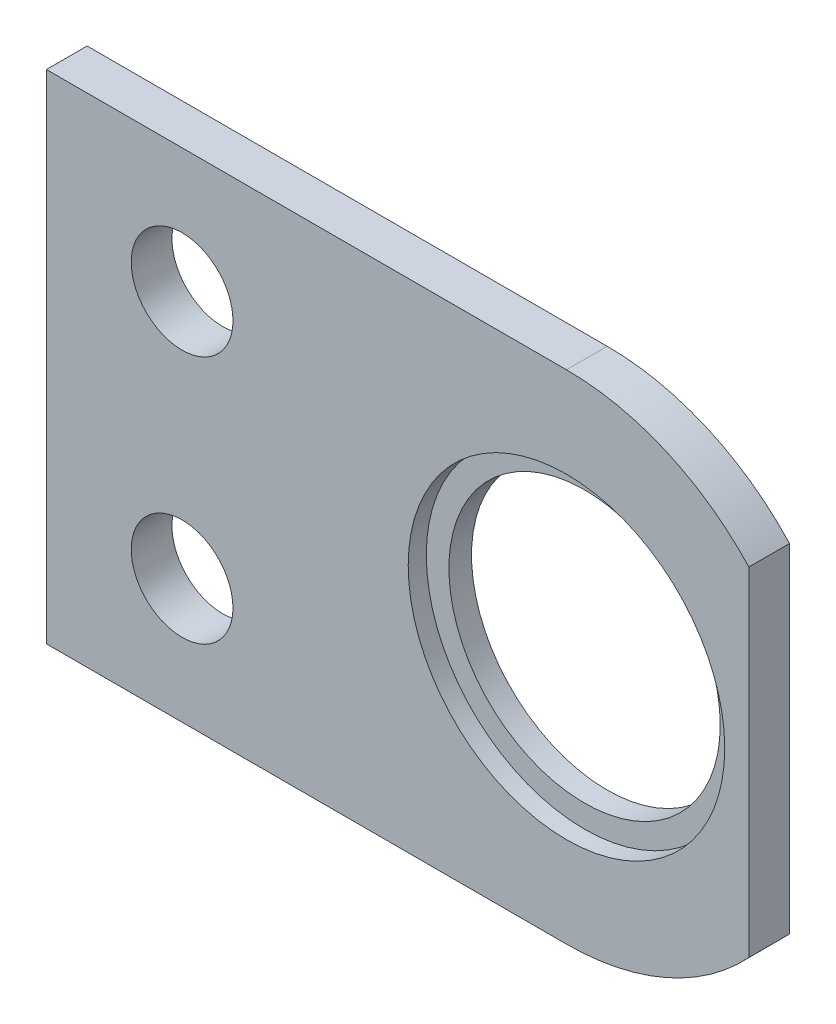
SolidWorks part; units mm, degrees
ref_plane "前视基准面" through (0, 0, 0) normal (0, 0, 1) x (1, 0, 0)
ref_plane "上视基准面" through (0, 0, 0) normal (0, 1, 0) x (1, 0, 0)
ref_plane "右视基准面" through (0, 0, 0) normal (1, 0, 0) x (0, 0, -1)
sketch "草图1" plane through (0, 0, 0) normal (0, 0, 1) x (1, 0, 0)
  line L0 (0, 7.4788) -> (0, -7.4788)
  line L1 (-31.0664, -11) -> (-8.0664, -11)
  line L2 (-31.0664, -11) -> (-31.0664, 11)
  line L3 (-8.0664, 11) -> (-31.0664, 11)
  line L4 (9.2449, 0) -> (-35.5118, 0) construction
  line L5 (-14.6664, 0) -> (-1.4664, 0) construction
  line L6 (-8.0664, -6.6) -> (-8.0664, 6.6) construction
  line L7 (-27.5414, 5.5) -> (-22.5914, 5.5) construction
  line L8 (-25.0664, 3.025) -> (-25.0664, 7.975) construction
  line L9 (-27.5414, -5.5) -> (-22.5914, -5.5) construction
  circle A0 centre (-25.0664, 5.5) radius 2.25
  arc A1 (-8.0664, -11) -> (0, -7.4788) centre (-8.0664, 0) ccw
  circle A2 centre (-25.0664, -5.5) radius 2.25
  arc A3 (0, 7.4788) -> (-8.0664, 11) centre (-8.0664, 0) ccw
  circle A4 centre (-8.0664, 0) radius 6
extrude "凸台-拉伸1" add sketch "草图1" along normal blind 1.8
sketch "草图2" plane through (0, 0, 1.8) normal (0, 0, 1) x (1, 0, 0)
  circle A0 centre (-8.0664, 0) radius 7
  dimension "D1" = 14
extrude "切除-拉伸1" cut sketch "草图2" against normal blind 0.8
